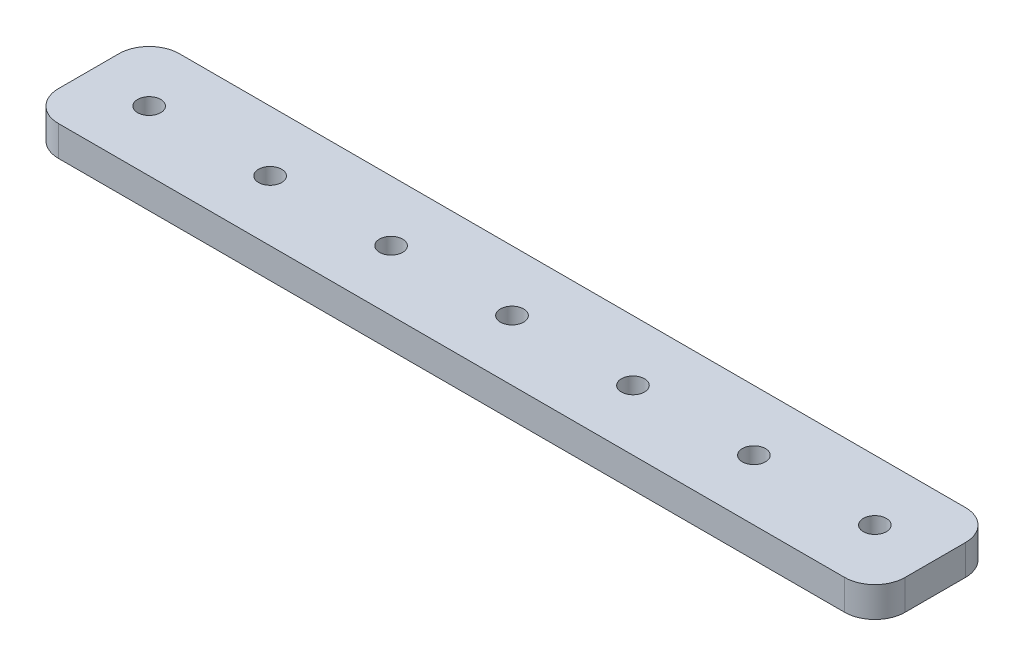
SolidWorks part; units mm, degrees
ref_plane "Front Plane" through (0, 0, 0) normal (0, 0, 1) x (1, 0, 0)
ref_plane "Top Plane" through (0, 0, 0) normal (0, 1, 0) x (1, 0, 0)
ref_plane "Right Plane" through (0, 0, 0) normal (1, 0, 0) x (0, 0, -1)
sketch "Sketch1" plane through (0, 0, 0) normal (0, 1, 0) x (1, 0, 0)
  line L1 (0, 0) -> (177.8, 0)
  line L2 (0, 0) -> (0, 25.4)
  line L3 (0, 25.4) -> (177.8, 25.4)
  line L4 (177.8, 0) -> (177.8, 25.4)
  dimension "D1" = 177.8
  dimension "D2" = 25.4
extrude "Boss-Extrude1" add sketch "Sketch1" along normal blind 6.35
sketch "Sketch2" plane through (0, 6.35, 0) normal (0, 1, 0) x (1, 0, 0)
  line L0 (0, 12.7) -> (177.8, 12.7) construction
  line L1 (0, 25.4) -> (0, 0) construction
  line L2 (177.8, 0) -> (177.8, 25.4) construction
  circle A0 centre (12.7, 12.7) radius 2.425
  circle A1 centre (38.1, 12.7) radius 2.425
  circle A2 centre (63.5, 12.7) radius 2.425
  circle A3 centre (88.9, 12.7) radius 2.425
  circle A4 centre (114.3, 12.7) radius 2.425
  circle A5 centre (139.7, 12.7) radius 2.425
  circle A6 centre (165.1, 12.7) radius 2.425
  point P8 (165.1, 12.7)
  dimension "D1" = 4.85
  dimension "D2" = 12.7
extrude "Cut-Extrude1" cut sketch "Sketch2" against normal blind 6.35
fillet "Fillet1" radius 6.35 4 edges at (177.8, 3.175, -25.4) (177.8, 3.175, 0) (0, 3.175, 0) (0, 3.175, -25.4)
